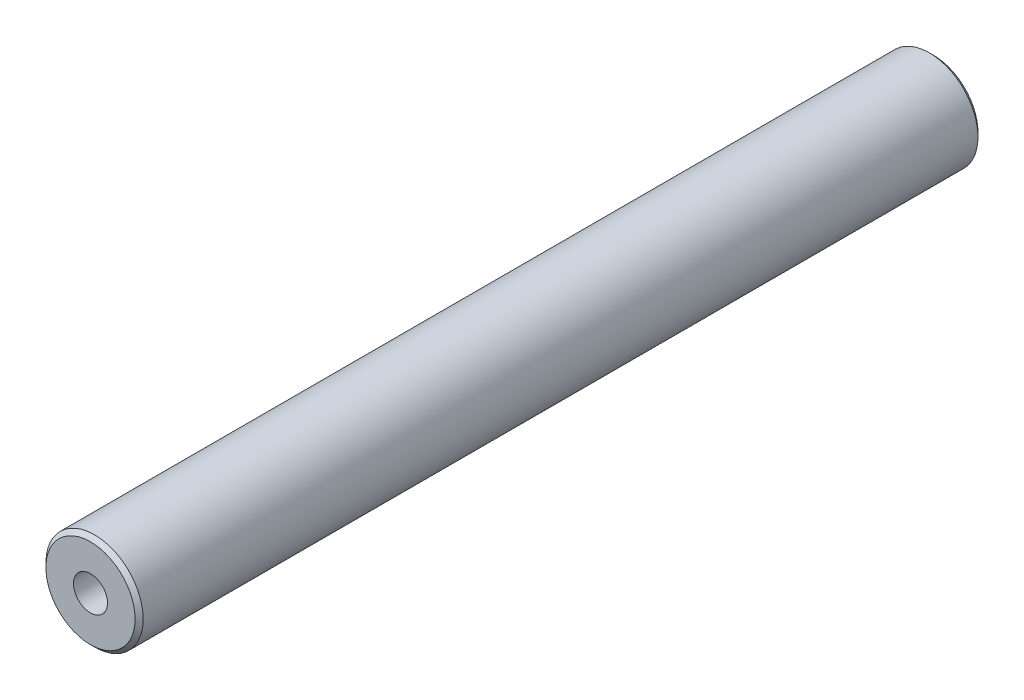
SolidWorks part; units mm, degrees
ref_plane "Plan de face" through (0, 0, 0) normal (0, 0, 1) x (1, 0, 0)
ref_plane "Plan de dessus" through (0, 0, 0) normal (0, 1, 0) x (1, 0, 0)
ref_plane "Plan de droite" through (0, 0, 0) normal (1, 0, 0) x (0, 0, -1)
sketch "Esquisse1" plane through (0, 0, 0) normal (0, 0, 1) x (1, 0, 0)
  circle A0 centre (0, 0) radius 6
extrude "Boss.-Extru.1" add sketch "Esquisse1" along normal blind 104
hole_wizard "Trou taraudé M5x0.81" positions "Esquisse2" profile "Esquisse3" tap size "M5x0.8" standard "Ansi Metric"
sketch "Esquisse2" plane through (0, 0, 0) normal (0, 0, -1) x (-1, 0, 0)
  point P0 (0, 0)
sketch "Esquisse3" plane through (0, 0, 0) normal (1, 0, 0) x (0, 1, 0)
  line L0 (0, 0) -> (0, 21.2618)
  line L1 (0, 21.2618) -> (2.1, 20)
  line L2 (2.1, 20) -> (2.1, 0)
  line L5 (2.1, 0) -> (0, 0)
  line L10 (0, 21.2618) -> (-2.1, 20) construction
  line L11 (0, -6.35) -> (0, 107.95) construction
  dimension "Diamètre du trou pour taraudage" = 4.2
  dimension "Profondeur du trou pour taraudage" = 20
  dimension "Angle de pointe" = 118
cosmetic thread "Filetage de perçage1" parameters "D1"=10, "D2"=5
hole_wizard "Trou taraudé M5x0.82" positions "Esquisse4" profile "Esquisse5" tap size "M5x0.8" standard "Ansi Metric"
sketch "Esquisse4" plane through (0, 0, 104) normal (0, 0, 1) x (1, 0, 0)
  point P0 (0, 0)
sketch "Esquisse5" plane through (0, 0, 104) normal (1, 0, 0) x (0, -1, 0)
  line L0 (0, 0) -> (0, 21.2618)
  line L1 (0, 21.2618) -> (2.1, 20)
  line L2 (2.1, 20) -> (2.1, 0)
  line L5 (2.1, 0) -> (0, 0)
  line L10 (0, 21.2618) -> (-2.1, 20) construction
  line L11 (0, -6.35) -> (0, 107.95) construction
  dimension "Diamètre du trou pour taraudage" = 4.2
  dimension "Profondeur du trou pour taraudage" = 20
  dimension "Angle de pointe" = 118
cosmetic thread "Filetage de perçage2" parameters "D1"=10, "D2"=5
chamfer "Chanfrein1" distance 0.5 angle 45 2 edges at (6, 0, 0) (6, 0, 104)
